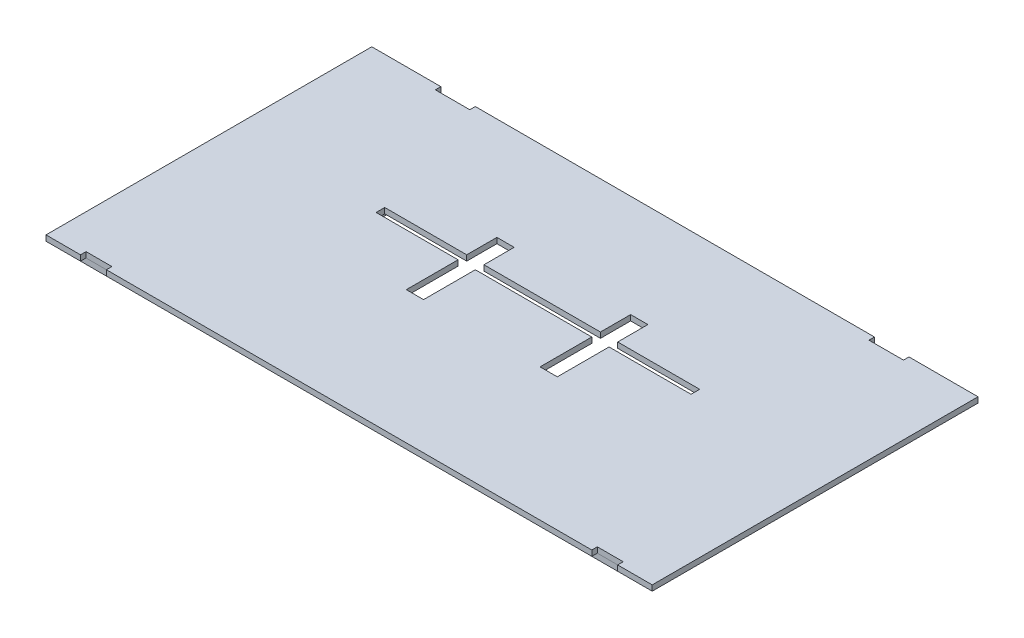
SolidWorks part; units mm, degrees
ref_plane "Front Plane" through (0, 0, 0) normal (0, 0, 1) x (1, 0, 0)
ref_plane "Top Plane" through (0, 0, 0) normal (0, 1, 0) x (1, 0, 0)
ref_plane "Right Plane" through (0, 0, 0) normal (1, 0, 0) x (0, 0, -1)
sketch "Sketch1" plane through (0, 0, 0) normal (0, 1, 0) x (1, 0, 0)
  line L0 (223.0755, 89.6522) -> (-223.0755, 89.6522) construction
  line L1 (-223.0755, -150.1238) -> (-197.6755, -150.1238)
  line L2 (-223.0755, -150.1238) -> (-223.0755, 89.6522)
  line L3 (-223.0755, 89.6522) -> (-172.2755, 89.6522)
  line L4 (223.0755, -150.1238) -> (223.0755, 89.6522)
  line L5 (-223.0755, -150.1238) -> (223.0755, 89.6522) construction
  line L6 (-223.0755, 89.6522) -> (223.0755, -150.1238) construction
  line L7 (-115.8875, -14.3608) -> (115.8875, -14.3608)
  line L8 (-115.8875, -14.3608) -> (-115.8875, -8.0108)
  line L9 (-115.8875, -8.0108) -> (115.8875, -8.0108)
  line L10 (115.8875, -14.3608) -> (115.8875, -8.0108)
  line L11 (-115.8875, -14.3608) -> (115.8875, -8.0108) construction
  line L12 (-115.8875, -8.0108) -> (115.8875, -14.3608) construction
  line L13 (-223.0755, -150.1238) -> (223.0755, -150.1238) construction
  line L14 (-178.6255, -150.1238) -> (178.6255, -150.1238)
  line L15 (-223.0755, 89.6522) -> (-223.0755, -150.1238) construction
  line L16 (-115.8875, -8.8045) -> (-115.8875, -19.1233) construction
  line L17 (-115.8875, -14.3608) -> (115.8875, -14.3608) construction
  line L18 (-197.6755, -150.1238) -> (-197.6755, -146.0598)
  line L19 (-197.6755, -146.0598) -> (-178.6255, -146.0598)
  line L20 (-178.6255, -146.0598) -> (-178.6255, -150.1238)
  line L21 (197.6755, -150.1238) -> (197.6755, -146.0598)
  line L22 (197.6755, -146.0598) -> (178.6255, -146.0598)
  line L23 (178.6255, -146.0598) -> (178.6255, -150.1238)
  line L24 (197.6755, -150.1238) -> (223.0755, -150.1238)
  line L25 (115.0938, -8.0108) -> (-115.0937, -8.0108) construction
  line L26 (172.2755, 85.5882) -> (223.0755, 85.5882) construction
  line L28 (-146.8755, 89.6522) -> (-146.8755, 85.5882)
  line L29 (-146.8755, 85.5882) -> (-172.2755, 85.5882)
  line L30 (-172.2755, 89.6522) -> (-172.2755, 85.5882)
  line L31 (172.2755, 89.6522) -> (223.0755, 89.6522)
  line L32 (-146.8755, 89.6522) -> (146.8755, 89.6522)
  line L33 (146.8755, 89.6522) -> (146.8755, 85.5882)
  line L34 (146.8755, 85.5882) -> (172.2755, 85.5882)
  line L35 (172.2755, 89.6522) -> (172.2755, 85.5882)
  point P0 (0, -30.2358)
  point P6 (0, -11.1858)
  dimension "D1" = 25.4
  dimension "D2" = 19.05
  dimension "D3" = 4.064
  dimension "D4" = 25.4
  dimension "D5" = 19.05
  dimension "D6" = 25.4
  dimension "D7" = 50.8
  dimension "D8" = 50.8
  dimension "D9" = 25.4
extrude "Boss-Extrude1" add sketch "Sketch1" along normal blind 4.064
sketch "Sketch2" plane through (0, 4.064, 0) normal (0, 1, 0) x (1, 0, 0)
  line L0 (115.8875, -14.3608) -> (115.8875, -8.0108) construction
  line L1 (55.5625, -52.4608) -> (42.8625, -52.4608)
  line L2 (55.5625, -52.4608) -> (55.5625, 14.2142)
  line L3 (55.5625, 14.2142) -> (42.8625, 14.2142)
  line L4 (42.8625, -52.4608) -> (42.8625, 14.2142)
  line L5 (-42.8625, -52.4608) -> (-55.5625, -52.4608)
  line L6 (-42.8625, -52.4608) -> (-42.8625, 14.2142)
  line L7 (-42.8625, 14.2142) -> (-55.5625, 14.2142)
  line L8 (-55.5625, -52.4608) -> (-55.5625, 14.2142)
  line L9 (-115.8875, -8.0108) -> (-115.8875, -14.3608) construction
  line L10 (115.8875, -8.0108) -> (-115.8875, -8.0108) construction
  line L11 (-115.8875, -14.3608) -> (115.8875, -14.3608) construction
  dimension "D1" = 12.7
  dimension "D2" = 12.7
  dimension "D3" = 73.025
  dimension "D4" = 73.025
  dimension "D5" = 22.225
  dimension "D6" = 38.1
extrude "Cut-Extrude1" cut sketch "Sketch2" against normal through all
sketch "Sketch3" plane through (0, 0, 0) normal (0, -1, 0) x (1, 0, 0)
  line L0 (93.1545, -7.9912) -> (93.1545, -85.5882)
  line L2 (223.0755, -85.5882) -> (-223.0755, -85.5882) construction
  line L3 (93.1545, -85.5882) -> (219.0115, -85.5882)
  line L4 (219.0115, 146.0598) -> (219.0115, -85.5882) construction
  line L5 (219.0115, -89.6522) -> (219.0115, -85.5882) construction
  line L6 (219.0115, -85.5882) -> (219.0115, 146.0598)
  line L7 (219.0115, 146.0598) -> (93.1545, 146.0598)
  line L8 (93.1545, 146.0598) -> (93.1545, 46.2378)
  line L10 (93.1545, 46.2378) -> (118.5545, 46.2378)
  line L11 (118.5545, 46.2378) -> (118.5545, -7.9912)
  line L12 (118.5545, -7.9912) -> (93.1545, -7.9912)
  line L14 (178.6255, 146.0598) -> (-178.6255, 146.0598) construction
  line L15 (-118.4275, 46.1108) -> (118.4275, 46.1108) construction
  line L16 (118.4275, 46.1108) -> (118.4275, 19.1233) construction
  line L17 (117.6337, -7.8642) -> (-117.6337, -7.8642) construction
  dimension "D1" = 25.4
  dimension "D2" = 0.127
  dimension "D3" = 0.127
  dimension "D4" = 0.127
extrude "Boss-Extrude2" add sketch "Sketch3" along normal blind 4.064 separate body
mirror "Mirror1" about plane through (0, 0, 0) normal (1, 0, 0) of bodies 103
